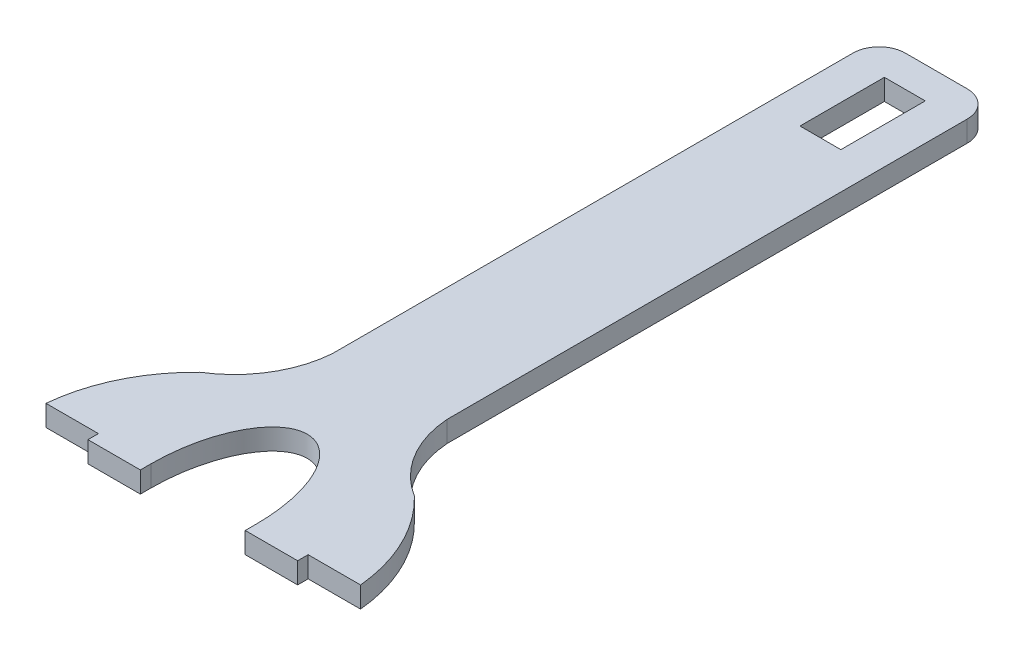
SolidWorks part; units mm, degrees
ref_plane "Front Plane" through (0, 0, 0) normal (0, 0, 1) x (1, 0, 0)
ref_plane "Top Plane" through (0, 0, 0) normal (0, 1, 0) x (1, 0, 0)
ref_plane "Right Plane" through (0, 0, 0) normal (1, 0, 0) x (0, 0, -1)
sketch "Sketch1" plane through (0, 0, 0) normal (0, 1, 0) x (1, 0, 0)
  line L0 (76.2, 0) -> (76.2, 13.2257) construction
  line L1 (0, 0) -> (25.4, 0)
  line L6 (48.5142, 90.3483) -> (48.5142, 342.4487)
  line L7 (61.2142, 355.1487) -> (91.1858, 355.1487)
  line L8 (103.8858, 90.3483) -> (103.8858, 342.4487)
  line L10 (127, 0) -> (152.4, 0)
  line L12 (25.4, 0) -> (25.4, -5.08)
  line L13 (25.4, -5.08) -> (50.8, -5.08)
  line L14 (50.8, 0) -> (50.8, -5.08)
  line L15 (127, -5.08) -> (101.6, -5.08)
  line L16 (101.6, 0) -> (101.6, -5.08)
  line L18 (127, 0) -> (127, -5.08)
  arc A0 (152.4, 0) -> (128.1429, 50.3487) centre (72.4725, -7.49) ccw
  arc A1 (128.1429, 50.3487) -> (103.8858, 90.3483) centre (155.2854, 94.1638) cw
  arc A2 (0, 0) -> (24.2571, 50.3487) centre (79.9275, -7.49) cw
  arc A3 (24.2571, 50.3487) -> (48.5142, 90.3483) centre (-2.8854, 94.1638) ccw
  arc A4 (91.1858, 355.1487) -> (103.8858, 342.4487) centre (91.1858, 342.4487) cw
  arc A5 (48.5142, 342.4487) -> (61.2142, 355.1487) centre (61.2142, 342.4487) cw
  ellipse E0 centre (76.2, 0) end of major axis (76.2, 50.3487) minor radius 25.4 (101.6, 0) -> (50.8, 0) ccw
  point P5 (76.2, 50.3487)
  dimension "D1" = 12.7
  dimension "D2" = 152.4
  dimension "D3" = 25.4
  dimension "D4" = 25.4
  dimension "D5" = 5.08
extrude "Boss-Extrude1" add sketch "Sketch1" along normal blind 10.16
sketch "Sketch2" plane through (0, 10.16, 0) normal (0, 1, 0) x (1, 0, 0)
  line L4 (91.1858, 355.1487) -> (61.2142, 355.1487) construction
  line L5 (86.1062, 299.0147) -> (66.2942, 299.0147)
  line L6 (86.1062, 299.0147) -> (86.1062, 339.9087)
  line L7 (86.1062, 339.9087) -> (66.2942, 339.9087)
  line L8 (66.2942, 299.0147) -> (66.2942, 339.9087)
  line L9 (86.1062, 299.0147) -> (66.2942, 339.9087) construction
  line L10 (86.1062, 339.9087) -> (66.2942, 299.0147) construction
  line L11 (48.5142, 342.4487) -> (48.5142, 90.3483) construction
  point P0 (76.2002, 319.4617)
  dimension "D1" = 19.812
  dimension "D2" = 15.24
  dimension "D3" = 40.894
  dimension "D4" = 17.78
extrude "Cut-Extrude1" cut sketch "Sketch2" against normal through all
